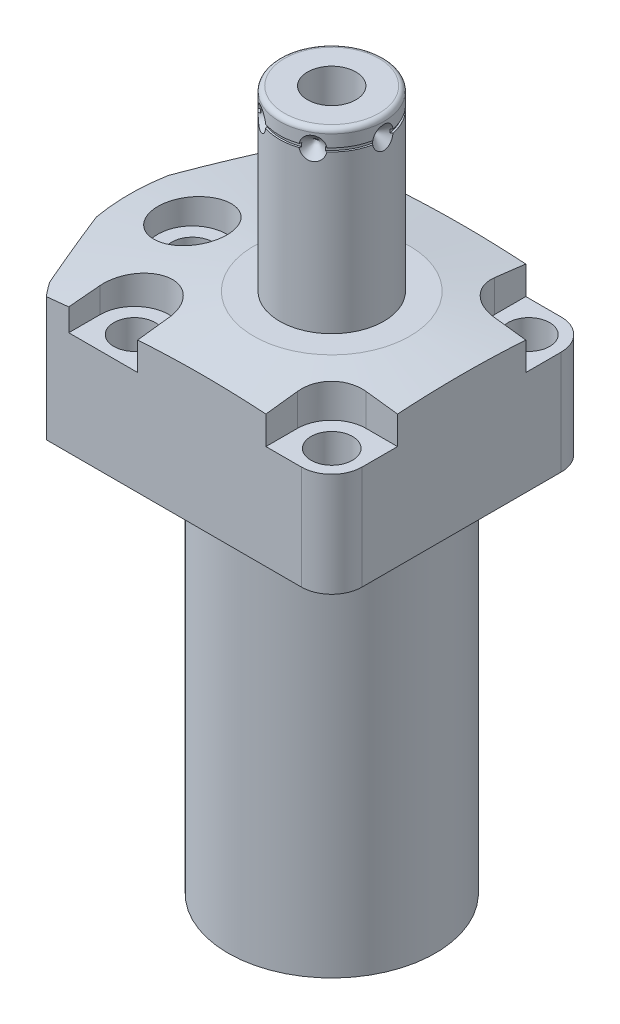
SolidWorks part; units mm, degrees
material "Alloy Steel"
ref_plane "Front Plane" through (0, 0, 0) normal (0, 0, 1) x (1, 0, 0)
ref_plane "Top Plane" through (0, 0, 0) normal (0, 1, 0) x (1, 0, 0)
ref_plane "Right Plane" through (0, 0, 0) normal (1, 0, 0) x (0, 0, -1)
sketch "S2D0002" plane through (0, 0, 0) normal (0, 0, 1) x (1, 0, 0)
  line L0 (-43.18, 0) -> (-43.18, 30.1498)
  line L1 (-43.18, 30.1498) -> (0, 30.1498)
  line L2 (0, 30.1498) -> (0, -80.9752)
  line L3 (0, -80.9752) -> (-22.098, -80.9752)
  line L4 (-22.098, -80.9752) -> (-22.098, 0)
  line L5 (-22.098, 0) -> (-43.18, 0)
  line L6 (0, -3.4925) -> (0, 73.3425) construction
  dimension "D1" = 111.125
  dimension "D2" = 44.196
  dimension "D3" = 86.36
  dimension "D4" = 80.9752
revolve "Revolve1" add sketch "S2D0002" angle 360 about L6
sketch "S2D0001" plane through (0, 0, 0) normal (0, -1, 0) x (1, 0, 0)
  line L0 (-33.136, -27.686) -> (33.136, -27.686)
  line L2 (33.136, 27.686) -> (-33.136, 27.686)
  line L3 (0, 0) -> (59.5614, 0) construction
  arc A0 (-33.136, -27.686) -> (33.136, -27.686) centre (0, 0) ccw
  circle A1 centre (0, 0) radius 43.18
  arc A2 (33.136, 27.686) -> (-33.136, 27.686) centre (0, 0) ccw
  point P4 (25.1041, 0)
  dimension "D1" = 55.372
  dimension "D2" = 0
extrude "Cut-Extrude1" cut sketch "S2D0001" against normal blind 32.9946
sketch "Sketch3" plane through (0, 30.1498, 0) normal (0, -1, 0) x (-1, 0, 0)
  line L0 (21.3317, 58.747) -> (45.6655, 0)
  line L1 (45.6655, 0) -> (21.3317, -58.747)
  line L2 (-32.7616, -13.5703) -> (61.25, 25.3706) construction
  line L3 (0, 0) -> (47.9453, 0) construction
  arc A0 (21.3317, -58.747) -> (21.3317, 58.747) centre (0, 0) ccw
  dimension "D3" = 125
  dimension "D1" = 22.5
  dimension "D2" = 42.1894
extrude "Cut-Extrude2" cut sketch "Sketch3" along normal up to surface (30.1498 mm away) up to face at (0, 0, -22.098)
sketch "Sketch4" plane through (0, 0, 0) normal (0, -1, 0) x (1, 0, 0)
  line L0 (27.686, -33.136) -> (27.686, 33.136)
  line L1 (-33.136, 27.686) -> (33.136, 27.686) construction
  arc A0 (27.686, -33.136) -> (27.686, 33.136) centre (0, 0) ccw
  arc A1 (33.136, -27.686) -> (33.136, 27.686) centre (0, 0) ccw construction
  dimension "D1" = 27.686
extrude "Cut-Extrude3" cut sketch "Sketch4" against normal blind 32.9946
fillet "Fillet1" radius 6.477 2 edges at (27.686, 15.0749, 27.686) (27.686, 15.0749, -27.686)
sketch "Sketch5" plane through (0, 30.1498, 0) normal (0, 1, 0) x (-1, 0, 0)
  line L0 (0, 0) -> (-37.3124, 0) construction
  line L1 (-27.686, 21.209) -> (-27.686, -21.209) construction
  line L2 (-21.209, -27.686) -> (33.136, -27.686) construction
  line L3 (-27.686, -13.6652) -> (-27.686, -27.686)
  line L4 (-27.686, -27.686) -> (-13.6652, -27.686)
  line L5 (-27.686, -13.6652) -> (-21.0058, -13.6652)
  line L6 (-13.6652, -21.0058) -> (-13.6652, -27.686)
  line L7 (-13.6652, 21.0058) -> (-13.6652, 27.686)
  line L8 (-27.686, 13.6652) -> (-21.0058, 13.6652)
  line L9 (0, 0.7832) -> (0, 0) construction
  line L10 (0, 0) -> (47.8281, 0) construction
  line L11 (-27.686, 27.686) -> (-13.6652, 27.686)
  line L12 (-27.686, 13.6652) -> (-27.686, 27.686)
  line L13 (0, 0) -> (0, 43.3168) construction
  line L14 (33.136, 27.686) -> (-21.209, 27.686) construction
  line L15 (13.6652, 27.686) -> (28.3464, 27.686)
  line L16 (13.6652, 27.686) -> (13.6652, 21.0058)
  line L17 (13.6652, -27.686) -> (13.6652, -21.0058)
  line L18 (28.3464, 27.686) -> (28.3464, 21.0058)
  line L19 (28.3464, -27.686) -> (28.3464, -21.0058)
  line L20 (13.6652, -27.686) -> (28.3464, -27.686)
  arc A0 (-13.6652, -21.0058) -> (-21.0058, -13.6652) centre (-21.0058, -21.0058) ccw
  arc A1 (-13.6652, 21.0058) -> (-21.0058, 13.6652) centre (-21.0058, 21.0058) cw
  arc A2 (28.3464, 21.0058) -> (13.6652, 21.0058) centre (21.0058, 21.0058) cw
  arc A3 (28.3464, -21.0058) -> (13.6652, -21.0058) centre (21.0058, -21.0058) ccw
  dimension "D3" = 21.0058
  dimension "D1" = 7.3406
  dimension "D2" = 21.0058
  dimension "D4" = 21.0058
extrude "Cut-Extrude4" cut sketch "Sketch5" against normal blind 8.001
sketch "S2D0003" plane through (0, 0, 0) normal (0, 0, 1) x (1, 0, 0)
  line L0 (-16.637, 30.1498) -> (-86.637, 20.3119)
  line L1 (0, 12.958) -> (0, 26.6311) construction
  line L2 (-16.637, 30.1498) -> (-86.637, 30.1498)
  line L3 (-86.637, 30.1498) -> (-86.637, 20.3119)
  line L4 (-33.136, 30.1498) -> (-28.3464, 30.1498) construction
  dimension "D1" = 33.274
  dimension "D2" = 8
  dimension "D3" = 70
revolve "Cut-Revolve1" cut sketch "S2D0003" angle 360 about L1
ref_plane "Plane20" through (0, 14.5034, 0) normal (0, -1, 0) x (1, 0, 0)
sketch "Sketch7" plane through (0, 14.5034, 0) normal (0, -1, 0) x (1, 0, 0)
  line L0 (-41.1733, -10.1813) -> (-42.8571, -6.1163)
  line L1 (-41.1733, -10.1813) -> (-41.0456, -10.1577)
  line L2 (-41.0456, -10.1577) -> (-40.5499, -10.363)
  line L3 (-40.5499, -10.363) -> (-27.9234, -5.133)
  line L4 (-27.9234, -5.133) -> (-25.6489, -10.6241)
  line L5 (-25.6489, -10.6241) -> (-38.9779, -16.1452)
  line L6 (0, 0) -> (22.0051, 9.1148) construction
  line L7 (-42.4971, -7.6492) -> (-35.4588, -24.6412) construction
  line L8 (-42.8571, -6.1163) -> (-43.0918, -6.2135)
  line L9 (-43.0918, -6.2135) -> (-38.9779, -16.1452)
  line L11 (-42.4971, -7.6492) -> (-35.4588, -24.6412) construction
  dimension "D1" = 14.1732
  dimension "D2" = 11.8872
  dimension "D3" = 45
  dimension "D4" = 0.254
  dimension "D5" = 0.5064
  dimension "D6" = 12.7
  dimension "D7" = 21.5
  dimension "D8" = 78
revolve "Cut-Revolve2" cut sketch "Sketch7" angle 360 about L6
ref_plane "Plane21" through (0, 0, -11.8364) normal (0, 0, 1) x (1, 0, 0)
sketch "Sketch9" plane through (0, 0, -11.8364) normal (0, 0, 1) x (1, 0, 0)
  line L0 (-31.8262, 1.5) -> (-33.575, 1.5)
  line L1 (-31.8262, 1.5) -> (-31.8262, 4.4972)
  line L2 (-31.8262, 4.4972) -> (-29.8196, 4.4972)
  line L3 (-29.8196, 4.4972) -> (-29.8196, 12.0664)
  line L4 (-29.8196, 12.0664) -> (-28.575, 12.0664)
  line L5 (-28.575, 12.0664) -> (-28.575, 0)
  line L6 (-28.575, -17.8934) -> (-28.575, 0.5283) construction
  line L7 (-33.136, 0) -> (21.209, 0) construction
  line L8 (-33.575, 0) -> (-33.575, 1.5)
  line L9 (-35.4588, 0) -> (-42.4971, 0) construction
  line L10 (-33.575, 0) -> (-28.575, 0)
  dimension "D1" = 7.5692
  dimension "D2" = 2.9972
  dimension "D3" = 28.575
  dimension "D4" = 2.4892
  dimension "D5" = 6.5024
  dimension "D6" = 10
  dimension "D7" = 1.5
revolve "Cut-Revolve4" cut sketch "Sketch9" angle 360 about L6
sketch "Sketch11" plane through (0, 4.4972, 0) normal (0, -1, 0) x (1, 0, 0)
  circle A0 centre (-28.575, -11.8364) radius 2.7432
  circle A1 centre (-28.575, -11.8364) radius 3.2512 construction
  dimension "D1" = 5.4864
extrude "Extrude1" add sketch "Sketch11" along normal blind 2.9972
sketch "Sketch12" plane through (0, 1.5, 0) normal (0, -1, 0) x (1, 0, 0)
  line L7 (-27.3304, -12.555) -> (-27.3304, -11.1178)
  line L8 (-27.3304, -11.1178) -> (-28.575, -10.3993)
  line L9 (-28.575, -10.3993) -> (-29.8196, -11.1178)
  line L10 (-29.8196, -11.1178) -> (-29.8196, -12.555)
  line L11 (-29.8196, -12.555) -> (-28.575, -13.2735)
  line L12 (-28.575, -13.2735) -> (-27.3304, -12.555)
  circle A0 centre (-28.575, -11.8364) radius 1.2446 construction
  circle A1 centre (-28.575, -11.8364) radius 2.7432 construction
  dimension "D2" = 2.4892
extrude "Cut-Extrude5" cut sketch "Sketch12" against normal blind 1.27
chamfer "Chamfer1" distance 0.254 angle 45 1 edges at (-28.575, 1.5, -14.5796)
mirror "Mirror2" about plane through (0, 0, 0) normal (0, 0, 1) of "Chamfer1", "Cut-Extrude5", "Extrude1", "Cut-Revolve4", "Cut-Revolve2"
sketch "Sketch16" plane through (-18.1864, 0, -11.8364) normal (0, 0, -1) x (-1, 0, 0)
  line L0 (10.3886, -0.4101) -> (10.3886, 1.5457) construction
  line L1 (5.3886, 1.5) -> (15.3886, 1.5) construction
  line L2 (7.1374, 4.4972) -> (7.1374, 1.5) construction
  line L3 (13.6398, 1.5) -> (13.6398, 4.4972) construction
  circle A0 centre (14.3886, 0.5) radius 1
  dimension "D2" = 2
  dimension "D1" = 8
  dimension "D3" = 1
revolve "Revolve3" add sketch "Sketch16" angle 360 about L0
mirror "Mirror3" about plane through (0, 0, 0) normal (0, 0, 1) of bodies 123 141
sketch "Sketch17" plane through (0, 0, 0) normal (1, 0, 0) x (0, 0, -1)
  line L0 (0, 30.1498) -> (-11.1125, 30.1498)
  line L1 (-11.1125, 30.1498) -> (-11.1125, 67.018)
  line L2 (-10.0965, 68.034) -> (0, 68.034)
  line L3 (0, 68.034) -> (0, 30.1498)
  line L4 (0, 24.9961) -> (0, 47.2925) construction
  line L5 (16.637, 30.1498) -> (-16.637, 30.1498) construction
  line L6 (-24.6412, 0) -> (-7.6492, 0) construction
  arc A0 (-10.0965, 68.034) -> (-11.1125, 67.018) centre (-10.0965, 67.018) ccw
  dimension "D2" = 1.016
  dimension "D1" = 22.225
  dimension "D3" = 68.034
revolve "Revolve4" add sketch "Sketch17" angle 360 about L4
sketch "Sketch18" plane through (0, 0, 0) normal (0, 0, 1) x (1, 0, 0)
  line L0 (5.1562, 68.034) -> (5.1562, 51.016)
  line L1 (5.1562, 51.016) -> (0, 47.9178)
  line L2 (5.1562, 68.034) -> (0, 68.034)
  line L3 (0, 68.034) -> (0, 47.9178)
  line L4 (0, -20.476) -> (0, 0.5839) construction
  line L5 (10.0965, 68.034) -> (-10.0965, 68.034) construction
  dimension "D1" = 17.018
  dimension "D2" = 10.3124
  dimension "D3" = 59
revolve "Cut-Revolve7" cut sketch "Sketch18" angle 360 about L4
sketch "Sketch19" plane through (-52.2568, 0, 16.5766) normal (-0.9239, 0, -0.3827) x (-0.3827, 0, 0.9239)
  circle A0 centre (-35.3126, 14.5034) radius 8.5
  circle A1 centre (-35.3126, 14.5034) radius 5.9436 construction
  dimension "D1" = 17
sketch "Sketch20" plane through (0, 0, 0) normal (0, 0, 1) x (1, 0, 0)
  line L3 (0, 64.0716) -> (4.3349, 64.0716) construction
  line L4 (-11.1125, 67.018) -> (-11.1125, 30.1498) construction
  line L5 (10.0965, 68.034) -> (-10.0965, 68.034) construction
  line L6 (-11.1125, 61.6586) -> (-11.1125, 64.0716)
  line L7 (-11.1125, 64.0716) -> (-8.6995, 64.0716)
  line L8 (-8.6995, 64.0716) -> (-11.1125, 61.6586)
  dimension "D1" = 3.9624
  dimension "D2" = 4.826
  dimension "D4" = 45
revolve "Cut-Revolve8" cut sketch "Sketch20" angle 360 about L3
sketch "Sketch22" plane through (0, 0, 0) normal (1, 0, 0) x (0, 0, -1)
  line L0 (11.1125, 64.453) -> (10.7315, 64.453)
  line L1 (10.7315, 64.453) -> (10.7315, 63.691)
  line L2 (10.7315, 63.691) -> (11.1125, 63.691)
  line L3 (11.1125, 63.691) -> (11.1125, 64.453)
  line L4 (0, 41.8979) -> (0, 49.0468) construction
  line L5 (5.1562, 68.034) -> (-5.1562, 68.034) construction
  line L6 (10.0965, 68.034) -> (-10.0965, 68.034) construction
  line L7 (11.1125, 30.1498) -> (11.1125, 67.018) construction
  dimension "D1" = 0.762
  dimension "D2" = 0.381
  dimension "D3" = 3.581
revolve "Cut-Revolve6" cut sketch "Sketch22" angle 360 about L4
hole_wizard "Hole1" positions "Sketch24" profile "Sketch23" legacy end condition up to next
sketch "Sketch24" plane through (0, 30.1498, 0) normal (0, 1, 0) x (-1, 0, 0)
  arc A0 (-13.6652, -21.0058) -> (-21.0058, -13.6652) centre (-21.0058, -21.0058) ccw construction
  arc A1 (-21.0058, 13.6652) -> (-13.6652, 21.0058) centre (-21.0058, 21.0058) ccw construction
  point P0 (29.6926, 0)
  point P1 (-21.0058, 21.0058)
  point P3 (-21.0058, -21.0058)
  point P15 (21.0058, 21.0058)
  point P18 (21.0058, -21.0058)
  dimension "D1" = 29.6926
sketch "Sketch23" plane through (-29.6926, 30.1498, 0) normal (1, 0, 0) x (0, 0, 1)
  line L0 (0, 0) -> (0, 30.1498)
  line L1 (0, 30.1498) -> (4.4196, 30.1498)
  line L2 (4.4196, 30.1498) -> (4.4196, 8.001)
  line L3 (4.4196, 8.001) -> (7.3406, 8.001)
  line L4 (7.3406, 8.001) -> (7.3406, 0)
  line L5 (7.3406, 0) -> (0, 0)
  line L6 (0, 110) -> (0, -10) construction
  dimension "Diameter" = 8.8392
  dimension "Depth" = 30.1498
  dimension "C-Bore Diameter" = 14.6812
  dimension "C-Bore Depth" = 8.001
sketch "Sketch25" plane through (0, -80.9752, 0) normal (0, -1, 0) x (1, 0, 0)
  circle A0 centre (0, 0) radius 11.3665
  dimension "D1" = 22.733
extrude "Cut-Extrude7" cut sketch "Sketch25" against normal blind 1.524
pattern_circular "CirPattern1" count 6 over 360 about axis through (0, -3.4925, 0) along (0, 1, 0) of "Cut-Revolve8"
